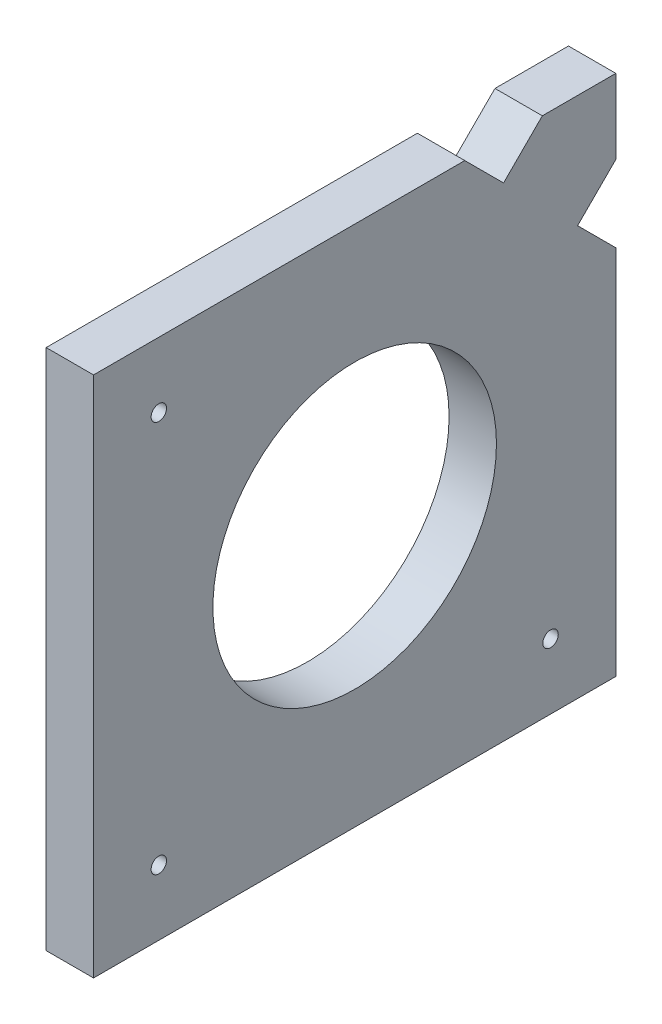
SolidWorks part; units mm, degrees
ref_plane "Front Plane" through (0, 0, 0) normal (0, 0, 1) x (1, 0, 0)
ref_plane "Top Plane" through (0, 0, 0) normal (0, 1, 0) x (1, 0, 0)
ref_plane "Right Plane" through (0, 0, 0) normal (1, 0, 0) x (0, 0, -1)
sketch "Sketch1" plane through (0, 0, 0) normal (1, 0, 0) x (0, 0, -1)
  line L0 (35, 70) -> (35, 0) construction
  line L1 (0, 0) -> (70, 0)
  line L2 (0, 0) -> (0, 70)
  line L3 (0, 70) -> (49.7566, 70)
  line L4 (70, 70) -> (70, 60.0116)
  line L5 (0, 35) -> (70, 35) construction
  line L6 (64.8725, 54.8841) -> (70, 49.7566)
  line L7 (54.9526, 64.804) -> (60.1486, 70)
  line L8 (70, 60.0116) -> (64.8725, 54.8841)
  line L10 (60.1486, 70) -> (70, 70)
  line L11 (70, 49.7566) -> (70, 0)
  line L12 (54.9526, 64.804) -> (49.7566, 70)
  circle A0 centre (35, 35) radius 19
extrude "Boss-Extrude1" add sketch "Sketch1" along normal blind 6.35
sketch "Sketch2" plane through (6.35, 0, 0) normal (1, 0, 0) x (0, 0, -1)
  circle A0 centre (8.75, 61.25) radius 1.0325
  circle A1 centre (8.75, 8.75) radius 1.0325
  circle A2 centre (61.25, 8.75) radius 1.0325
extrude "Cut-Extrude1" cut sketch "Sketch2" against normal blind 6.35
sketch "Sketch3" plane through (6.35, 0, 0) normal (1, 0, 0) x (0, 0, -1)
  line L0 (70, 70) -> (48.435, 48.435)
  circle A0 centre (35, 35) radius 19 construction
